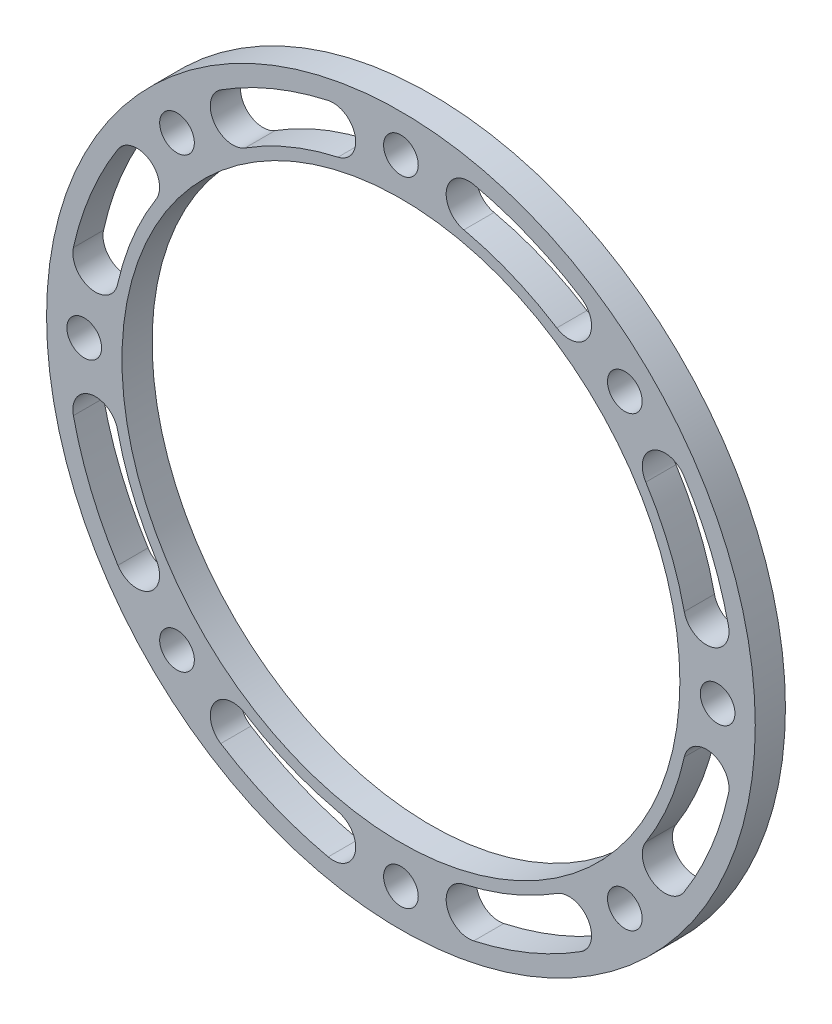
SolidWorks part; units mm, degrees
material "Hexcel AS4C (3000 丝)"
ref_plane "前视基准面" through (0, 0, 0) normal (0, 0, 1) x (1, 0, 0)
ref_plane "上视基准面" through (0, 0, 0) normal (0, 1, 0) x (1, 0, 0)
ref_plane "右视基准面" through (0, 0, 0) normal (1, 0, 0) x (0, 0, -1)
sketch "草图1" plane through (0, 0, 0) normal (0, 0, 1) x (1, 0, 0)
  circle A0 centre (0, 0) radius 47
  circle A1 centre (0, 0) radius 42 construction
  circle A2 centre (0, 0) radius 37
  circle A3 centre (0, 42) radius 2.3
  circle A4 centre (29.6985, 29.6985) radius 2.3
  circle A5 centre (42, 0) radius 2.3
  circle A6 centre (29.6985, -29.6985) radius 2.3
  circle A7 centre (0, -42) radius 2.3
  circle A8 centre (-29.6985, -29.6985) radius 2.3
  circle A9 centre (-42, 0) radius 2.3
  circle A10 centre (-29.6985, 29.6985) radius 2.3
  dimension "D1" = 94
  dimension "D2" = 84
  dimension "D3" = 4.6
  dimension "D5" = 74
  dimension "D4" = 8
extrude "凸台-拉伸1" add sketch "草图1" along normal blind 4
sketch "草图3" plane through (0, 0, 4) normal (0, 0, 1) x (1, 0, 0)
  line L0 (0, 0) -> (0, 42) construction
  line L1 (0, 0) -> (29.6985, 29.6985) construction
  circle A0 centre (0, 0) radius 41.5 construction
  arc A1 (9, 40.5123) -> (22.2826, 35.0105) centre (0, 0) cw construction
  arc A2 (23.8934, 37.5414) -> (9.6506, 43.4409) centre (0, 0) ccw
  arc A3 (20.6718, 32.4796) -> (8.3494, 37.5837) centre (0, 0) ccw
  arc A4 (20.6718, 32.4796) -> (23.8934, 37.5414) centre (22.2826, 35.0105) ccw
  arc A5 (9.6506, 43.4409) -> (8.3494, 37.5837) centre (9, 40.5123) ccw
  arc A6 (35.0105, 22.2826) -> (40.5123, 9) centre (0, 0) cw construction
  arc A7 (43.4409, 9.6506) -> (37.5414, 23.8934) centre (0, 0) ccw
  arc A8 (37.5837, 8.3494) -> (32.4796, 20.6718) centre (0, 0) ccw
  arc A9 (37.5837, 8.3494) -> (43.4409, 9.6506) centre (40.5123, 9) ccw
  arc A10 (37.5414, 23.8934) -> (32.4796, 20.6718) centre (35.0105, 22.2826) ccw
  arc A11 (40.5123, -9) -> (35.0105, -22.2826) centre (0, 0) cw construction
  arc A12 (37.5414, -23.8934) -> (43.4409, -9.6506) centre (0, 0) ccw
  arc A13 (32.4796, -20.6718) -> (37.5837, -8.3494) centre (0, 0) ccw
  arc A14 (32.4796, -20.6718) -> (37.5414, -23.8934) centre (35.0105, -22.2826) ccw
  arc A15 (43.4409, -9.6506) -> (37.5837, -8.3494) centre (40.5123, -9) ccw
  arc A16 (22.2826, -35.0105) -> (9, -40.5123) centre (0, 0) cw construction
  arc A17 (9.6506, -43.4409) -> (23.8934, -37.5414) centre (0, 0) ccw
  arc A18 (8.3494, -37.5837) -> (20.6718, -32.4796) centre (0, 0) ccw
  arc A19 (8.3494, -37.5837) -> (9.6506, -43.4409) centre (9, -40.5123) ccw
  arc A20 (23.8934, -37.5414) -> (20.6718, -32.4796) centre (22.2826, -35.0105) ccw
  arc A21 (-9, -40.5123) -> (-22.2826, -35.0105) centre (0, 0) cw construction
  arc A22 (-23.8934, -37.5414) -> (-9.6506, -43.4409) centre (0, 0) ccw
  arc A23 (-20.6718, -32.4796) -> (-8.3494, -37.5837) centre (0, 0) ccw
  arc A24 (-20.6718, -32.4796) -> (-23.8934, -37.5414) centre (-22.2826, -35.0105) ccw
  arc A25 (-9.6506, -43.4409) -> (-8.3494, -37.5837) centre (-9, -40.5123) ccw
  arc A26 (-35.0105, -22.2826) -> (-40.5123, -9) centre (0, 0) cw construction
  arc A27 (-43.4409, -9.6506) -> (-37.5414, -23.8934) centre (0, 0) ccw
  arc A28 (-37.5837, -8.3494) -> (-32.4796, -20.6718) centre (0, 0) ccw
  arc A29 (-37.5837, -8.3494) -> (-43.4409, -9.6506) centre (-40.5123, -9) ccw
  arc A30 (-37.5414, -23.8934) -> (-32.4796, -20.6718) centre (-35.0105, -22.2826) ccw
  arc A31 (-40.5123, 9) -> (-35.0105, 22.2826) centre (0, 0) cw construction
  arc A32 (-37.5414, 23.8934) -> (-43.4409, 9.6506) centre (0, 0) ccw
  arc A33 (-32.4796, 20.6718) -> (-37.5837, 8.3494) centre (0, 0) ccw
  arc A34 (-32.4796, 20.6718) -> (-37.5414, 23.8934) centre (-35.0105, 22.2826) ccw
  arc A35 (-43.4409, 9.6506) -> (-37.5837, 8.3494) centre (-40.5123, 9) ccw
  arc A36 (-22.2826, 35.0105) -> (-9, 40.5123) centre (0, 0) cw construction
  arc A37 (-9.6506, 43.4409) -> (-23.8934, 37.5414) centre (0, 0) ccw
  arc A38 (-8.3494, 37.5837) -> (-20.6718, 32.4796) centre (0, 0) ccw
  arc A39 (-8.3494, 37.5837) -> (-9.6506, 43.4409) centre (-9, 40.5123) ccw
  arc A40 (-23.8934, 37.5414) -> (-20.6718, 32.4796) centre (-22.2826, 35.0105) ccw
  point P5 (15.8814, 38.341)
  point P20 (38.341, 15.8814)
  point P27 (38.341, -15.8814)
  point P34 (15.8814, -38.341)
  point P41 (-15.8814, -38.341)
  point P48 (-38.341, -15.8814)
  point P55 (-38.341, 15.8814)
  point P62 (-15.8814, 38.341)
  dimension "D1" = 83
  dimension "D2" = 3
  dimension "D3" = 9
  dimension "D4" = 9
  dimension "D5" = 8
extrude "切除-拉伸1" cut sketch "草图3" against normal through all contours A3 A5 A2 A4 | A37 A40 A38 A39 | A32 A35 A33 A34 | A27 A30 A28 A29 | A22 A25 A23 A24 | A17 A20 A18 A19 | A7 A10 A8 A9 | A12 A15 A13 A14
move or copy body "实体-移动/复制1" bodies to move or copy 108
